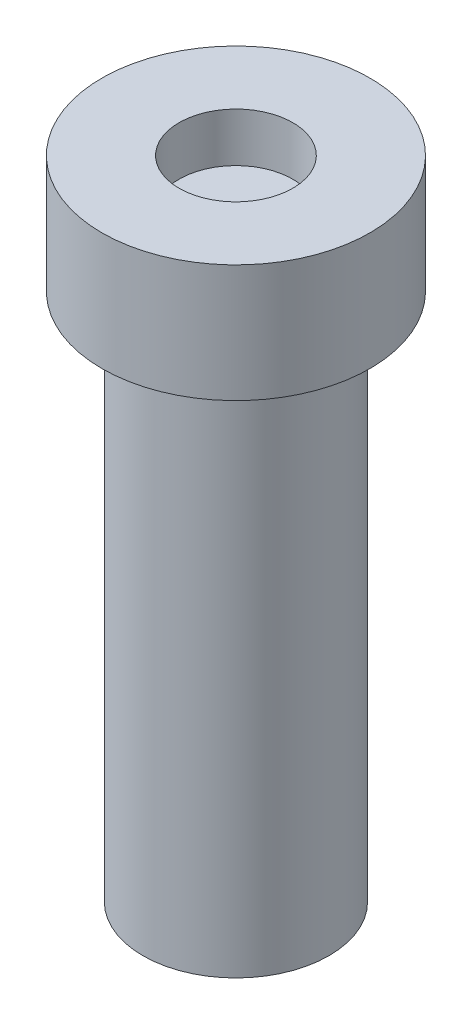
SolidWorks part; units mm, degrees
ref_plane "Front Plane" through (0, 0, 0) normal (0, 0, 1) x (1, 0, 0)
ref_plane "Top Plane" through (0, 0, 0) normal (0, 1, 0) x (1, 0, 0)
ref_plane "Right Plane" through (0, 0, 0) normal (1, 0, 0) x (0, 0, -1)
sketch "Sketch1" plane through (0, 0, 0) normal (0, 0, 1) x (1, 0, 0)
  line L0 (0, 0) -> (0, -3.8796) construction
  line L1 (2.9024, 31.0602) -> (6.8421, 31.0602)
  line L2 (6.8421, 31.0602) -> (6.8421, 25.0602)
  line L3 (6.8421, 25.0602) -> (4.75, 25.0602)
  line L4 (4.75, 25.0602) -> (4.75, -1.9398)
  line L5 (4.75, -1.9398) -> (0, -1.9398)
  line L6 (2.9024, 31.0602) -> (2.9024, 28.5602)
  line L7 (2.9024, 28.5602) -> (0, 28.5602)
  line L8 (0, 28.5602) -> (0, -1.9398)
  point P10 (0, 8.0262)
  dimension "D1" = 9.5
  dimension "D2" = 27
  dimension "D3" = 6
  dimension "D4" = 2.5
revolve "Revolve1" add sketch "Sketch1" angle 360 about L0
